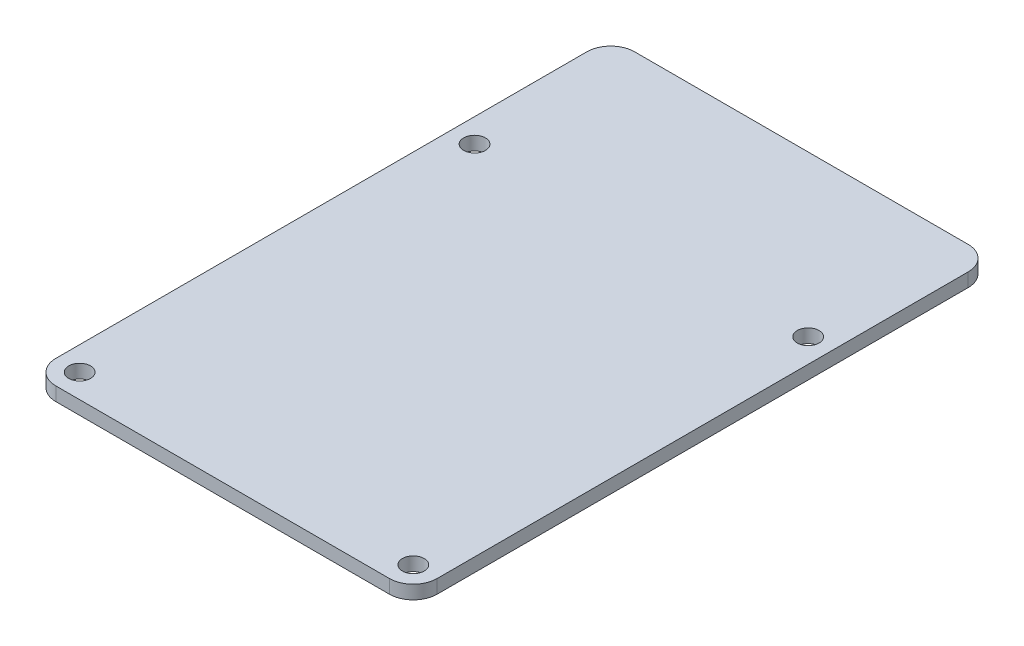
SolidWorks part; units mm, degrees
ref_plane "Front Plane" through (0, 0, 0) normal (0, 0, 1) x (1, 0, 0)
ref_plane "Top Plane" through (0, 0, 0) normal (0, 1, 0) x (1, 0, 0)
ref_plane "Right Plane" through (0, 0, 0) normal (1, 0, 0) x (0, 0, -1)
sketch "Sketch1" plane through (0, 0, 0) normal (0, 1, 0) x (1, 0, 0)
  line L1 (-28, -42.5) -> (28, -42.5)
  line L2 (-28, -42.5) -> (-28, 42.5)
  line L3 (-28, 42.5) -> (28, 42.5)
  line L4 (28, -42.5) -> (28, 42.5)
  line L5 (-28, -42.5) -> (28, 42.5) construction
  line L6 (-28, 42.5) -> (28, -42.5) construction
  point P0 (0, 0)
  dimension "D1" = 85
  dimension "D2" = 56
extrude "Boss-Extrude1" add sketch "Sketch1" along normal blind 2
hole_wizard "M3 Clearance Hole1" positions "Sketch3" profile "Sketch4" hole size "M3" standard "ISO" end condition up to next
sketch "Sketch3" plane through (0, 2, 0) normal (0, 1, 0) x (1, 0, 0)
  line L1 (-24.5, 19) -> (24.5, 19) construction
  line L2 (-24.5, 19) -> (-24.5, -39) construction
  line L3 (-24.5, -39) -> (24.5, -39) construction
  line L4 (24.5, 19) -> (24.5, -39) construction
  line L5 (28, -42.5) -> (28, 42.5) construction
  line L6 (-28, -42.5) -> (28, -42.5) construction
  point P1 (-24.5, 19)
  point P2 (24.5, -39)
  point P241 (-24.5, -39)
  point P242 (24.5, 19)
  dimension "D1" = 3.5
  dimension "D2" = 3.5
  dimension "D3" = 49
  dimension "D4" = 58
sketch "Sketch4" plane through (-24.5, 2, -19) normal (1, 0, 0) x (0, 0, 1)
  line L0 (0, 0) -> (0, 2)
  line L1 (0, 2) -> (1.6, 2)
  line L2 (1.6, 2) -> (1.6, 0)
  line L5 (1.6, 0) -> (0, 0)
  line L11 (0, -6.35) -> (0, 107.95) construction
  dimension "Thru Hole Dia." = 3.2
  dimension "Thru Hole Depth" = 2
fillet "Verrundung1" radius 3.5 4 edges at (-28, 1, -42.5) (28, 1, -42.5) (-28, 1, 42.5) (28, 1, 42.5)
